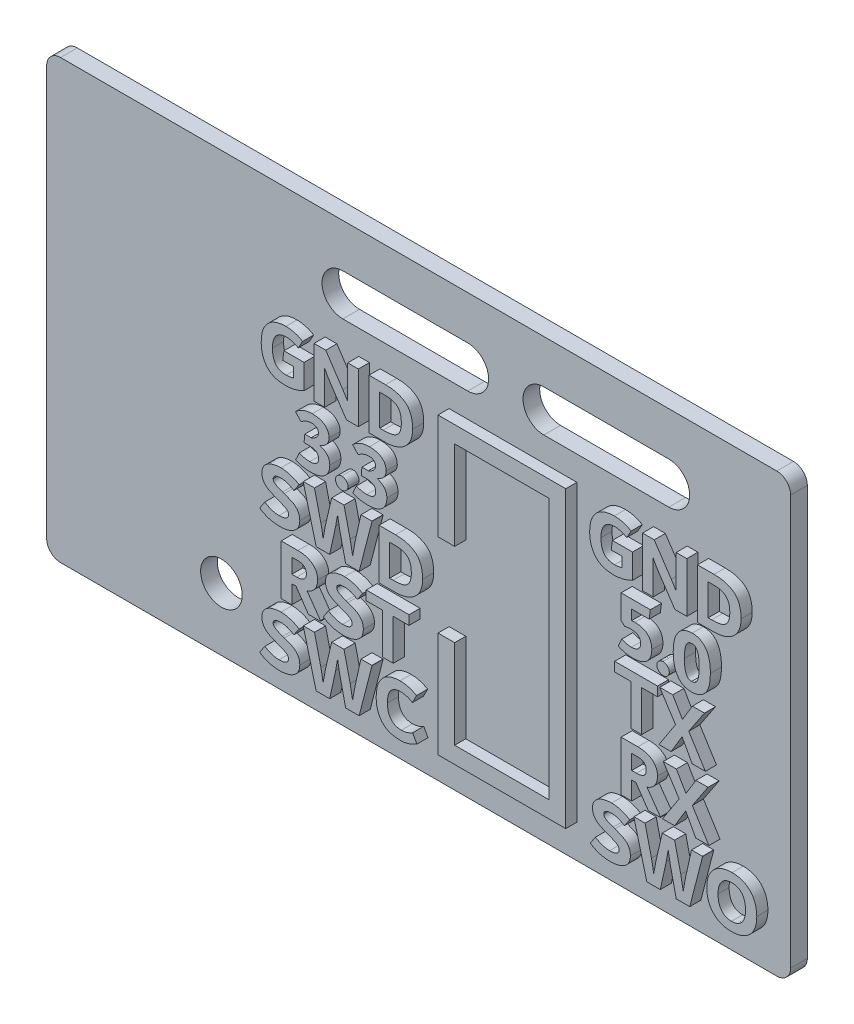
SolidWorks part; units mm, degrees
ref_plane "Спереди" through (0, 0, 0) normal (0, 0, 1) x (1, 0, 0)
ref_plane "Сверху" through (0, 0, 0) normal (0, 1, 0) x (1, 0, 0)
ref_plane "Справа" through (0, 0, 0) normal (1, 0, 0) x (0, 0, -1)
sketch "Эскиз1" plane through (0, 0, 0) normal (0, 0, 1) x (1, 0, 0)
  line L0 (0, 26.865) -> (53.584, 26.865) construction
  line L1 (0, 0) -> (53.584, 0)
  line L2 (0, 0) -> (0, 31.505)
  line L3 (0, 31.505) -> (53.584, 31.505)
  line L4 (53.584, 0) -> (53.584, 31.505)
  line L5 (0, 4.513) -> (53.584, 4.513) construction
  line L6 (12.586, 31.505) -> (12.586, 0) construction
  line L7 (30.33, 31.505) -> (30.33, 0) construction
  line L8 (44.808, 31.505) -> (44.808, 0) construction
  line L9 (35.808, 31.505) -> (35.808, 0) construction
  line L10 (21.33, 31.505) -> (21.33, 0) construction
  line L11 (21.33, 26.865) -> (30.33, 26.865) construction
  line L12 (21.33, 28.365) -> (30.33, 28.365)
  line L13 (21.33, 25.365) -> (30.33, 25.365)
  line L14 (35.808, 26.865) -> (44.808, 26.865) construction
  line L15 (35.808, 28.365) -> (44.808, 28.365)
  line L16 (35.808, 25.365) -> (44.808, 25.365)
  arc A0 (21.33, 28.365) -> (21.33, 25.365) centre (21.33, 26.865) ccw
  arc A1 (30.33, 25.365) -> (30.33, 28.365) centre (30.33, 26.865) ccw
  arc A2 (35.808, 28.365) -> (35.808, 25.365) centre (35.808, 26.865) ccw
  arc A3 (44.808, 25.365) -> (44.808, 28.365) centre (44.808, 26.865) ccw
  circle A4 centre (12.586, 4.513) radius 1.5
  point P21 (25.83, 26.865)
  point P26 (40.308, 26.865)
  dimension "D10" = 3
  dimension "D1" = 53.584
  dimension "D2" = 31.505
  dimension "D3" = 12.586
  dimension "D4" = 4.513
  dimension "D5" = 4.64
  dimension "D6" = 9
  dimension "D7" = 9
  dimension "D8" = 8.776
  dimension "D9" = 23.254
  dimension "D11" = 3
  dimension "D12" = 3
extrude "Бобышка-Вытянуть1" add sketch "Эскиз1" along normal blind 1.2
fillet "Скругление1" radius 1 4 edges at (0, 31.505, 0.6) (0, 0, 0.6) (53.584, 0, 0.6) (53.584, 31.505, 0.6)
sketch "Эскиз2" plane through (0, 0, 1.2) normal (0, 0, 1) x (1, 0, 0)
  line L0 (29.584, 16) -> (29.584, 23)
  line L1 (29.584, 23) -> (37.584, 23)
  line L2 (37.584, 23) -> (37.584, 3)
  line L3 (37.584, 3) -> (29.584, 3)
  line L4 (29.584, 3) -> (29.584, 10)
  line L5 (1, 0) -> (52.584, 0) construction
  line L6 (53.584, 1) -> (53.584, 30.505) construction
  dimension "D1" = 3
  dimension "D2" = 20
  dimension "D3" = 8
  dimension "D4" = 7
  dimension "D5" = 7
  dimension "D6" = 16
extrude "Вытянуть-Тонкостенный1" add sketch "Эскиз2" along normal blind 0.8 thin thin type mid plane wall 1.2
sketch "Эскиз3" plane through (0, 0, 1.2) normal (0, 0, 1) x (1, 0, 0)
  line L0 (0, 2) -> (53.584, 2) construction
  line L1 (0, 30.505) -> (0, 1) construction
  line L2 (53.584, 1) -> (53.584, 30.505) construction
  line L3 (1, 0) -> (52.584, 0) construction
  line L4 (0, 6.5) -> (53.584, 6.5) construction
  line L5 (0, 11) -> (53.584, 11) construction
  line L6 (0, 15.5) -> (53.584, 15.5) construction
  line L7 (0, 20) -> (53.584, 20) construction
  text T0 "             GND          GND" font "Dubai" height 3.6
  text T1 "               3.3             5.0" font "Dubai" height 3.6
  text T2 "             SWD           TX" font "Dubai" height 3.6
  text T3 "              RST            RX" font "Dubai" height 3.6
  text T4 "             SWC          SWO" font "Dubai" height 3.6
  dimension "D1" = 2
  dimension "D2" = 5
extrude "Бобышка-Вытянуть2" add sketch "Эскиз3" along normal blind 0.8
